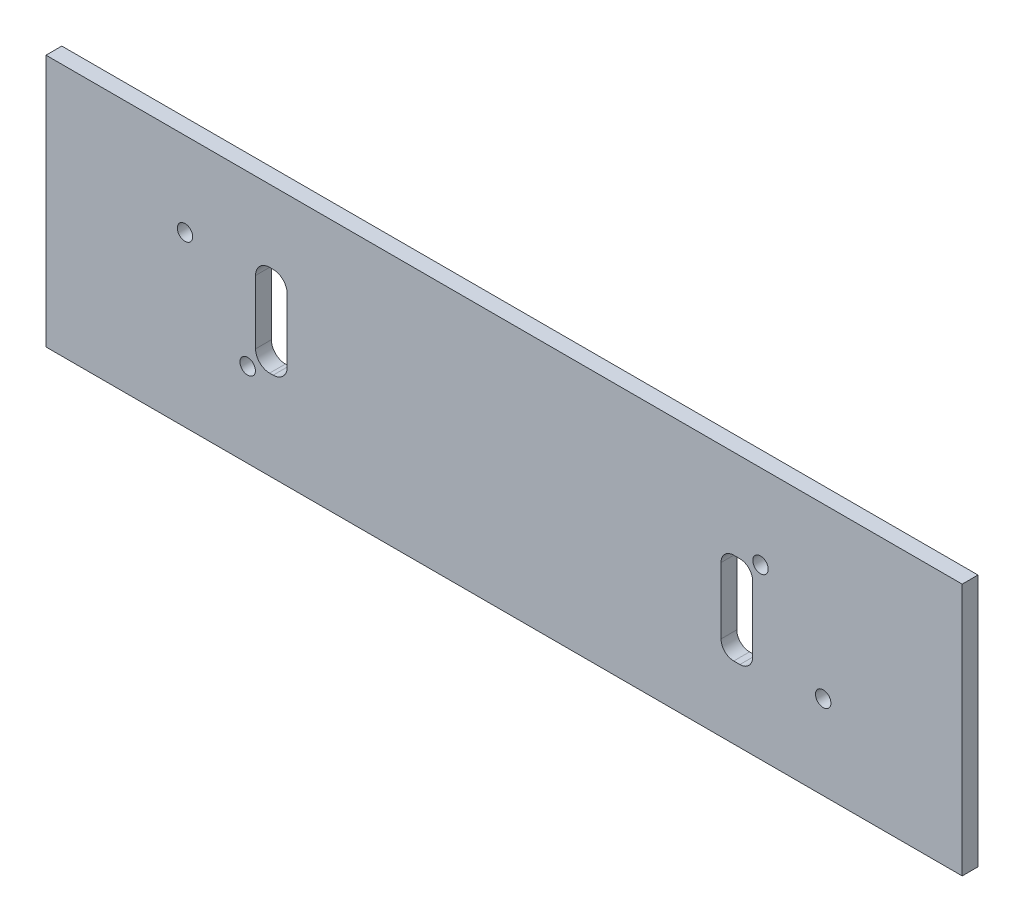
SolidWorks part; units mm, degrees
ref_plane "Front Plane" through (0, 0, 0) normal (0, 0, 1) x (1, 0, 0)
ref_plane "Top Plane" through (0, 0, 0) normal (0, 1, 0) x (1, 0, 0)
ref_plane "Right Plane" through (0, 0, 0) normal (1, 0, 0) x (0, 0, -1)
sketch "Sketch2" plane through (0, 0, 0) normal (0, 0, 1) x (1, 0, 0)
  line L1 (-92.075, -25.4) -> (92.075, -25.4)
  line L2 (-92.075, -25.4) -> (-92.075, 25.4)
  line L3 (-92.075, 25.4) -> (92.075, 25.4)
  line L4 (92.075, -25.4) -> (92.075, 25.4)
  line L5 (-92.075, -25.4) -> (92.075, 25.4) construction
  line L6 (-92.075, 25.4) -> (92.075, -25.4) construction
  point P0 (0, 0)
  dimension "D1" = 184.15
  dimension "D2" = 50.8
extrude "Boss-Extrude1" add sketch "Sketch2" along normal mid plane 3.175
sketch "Sketch3" plane through (0, 0, -1.5875) normal (0, 0, -1) x (-1, 0, 0)
  line L0 (-47.975, 5.89) -> (-47.975, -9.35) construction
  line L1 (-47.975, -1.73) -> (-45.575, -1.73) construction
  line L2 (-46.775, -11.05) -> (-46.775, 11.05) construction
  line L3 (-46.1593, -10.9375) -> (-47.3907, -10.9375)
  line L4 (-43.6, -8.3782) -> (-43.6, 4.9182)
  line L5 (-46.1593, 7.4775) -> (-47.3907, 7.4775)
  line L6 (-49.95, -8.3782) -> (-49.95, 4.9182)
  line L7 (-43.6, -10.9375) -> (-49.95, 7.4775) construction
  line L8 (-43.6, 7.4775) -> (-49.95, -10.9375) construction
  line L9 (47.975, 9.35) -> (47.975, -5.89) construction
  line L10 (47.975, 1.73) -> (43.6, 1.73) construction
  line L11 (46.775, 11.05) -> (46.775, -11.05) construction
  line L12 (46.4193, -7.4775) -> (47.1307, -7.4775)
  line L13 (43.6, -4.6582) -> (43.6, 8.1182)
  line L14 (46.4193, 10.9375) -> (47.1307, 10.9375)
  line L15 (49.95, -4.6582) -> (49.95, 8.1182)
  line L16 (43.6, -7.4775) -> (49.95, 10.9375) construction
  line L17 (43.6, 10.9375) -> (49.95, -7.4775) construction
  circle A0 centre (-51.535, 8.49) radius 1.55
  circle A1 centre (-64.135, -8.51) radius 1.55
  circle A2 centre (64.135, 8.51) radius 1.55
  circle A3 centre (51.535, -8.49) radius 1.55
  arc A4 (-47.3907, -10.9375) -> (-49.95, -8.3782) centre (-47.3907, -8.3782) cw
  arc A5 (-46.1593, -10.9375) -> (-43.6, -8.3782) centre (-46.1593, -8.3782) ccw
  arc A6 (-46.1593, 7.4775) -> (-43.6, 4.9182) centre (-46.1593, 4.9182) cw
  arc A7 (-47.3907, 7.4775) -> (-49.95, 4.9182) centre (-47.3907, 4.9182) ccw
  arc A9 (46.4193, -7.4775) -> (43.6, -4.6582) centre (46.4193, -4.6582) cw
  arc A10 (47.1307, -7.4775) -> (49.95, -4.6582) centre (47.1307, -4.6582) ccw
  arc A11 (47.1307, 10.9375) -> (49.95, 8.1182) centre (47.1307, 8.1182) cw
  arc A12 (46.4193, 10.9375) -> (43.6, 8.1182) centre (46.4193, 8.1182) ccw
  point P18 (-46.775, -1.73)
  point P43 (46.775, 1.73)
  point P61 (46.775, 1.73)
  point P64 (43.6, 1.73)
  dimension "D1" = 3.1
  dimension "D4" = 2.5593
  dimension "D7" = 2.8193
  dimension "D2" = 6.35
  dimension "D3" = 18.415
  dimension "D5" = 6.35
  dimension "D6" = 18.415
extrude "Cut-Extrude1" cut sketch "Sketch3" against normal blind 5.08
